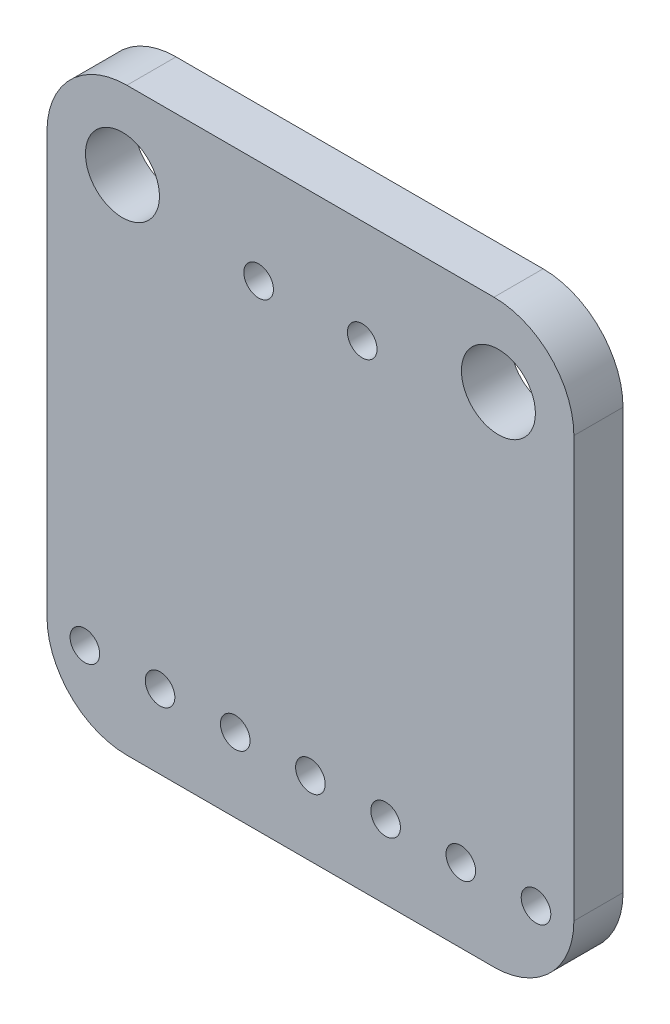
SolidWorks part; units mm, degrees
ref_plane "Front" through (0, 0, 0) normal (0, 0, 1) x (1, 0, 0)
ref_plane "Top" through (0, 0, 0) normal (0, 1, 0) x (1, 0, 0)
ref_plane "Right" through (0, 0, 0) normal (1, 0, 0) x (0, 0, -1)
sketch "Sketch1" plane through (0, 0, 0) normal (0, 0, 1) x (1, 0, 0)
  line L1 (8.9, -9.8) -> (-8.9, -9.8)
  line L2 (8.9, -9.8) -> (8.9, 9.8)
  line L3 (8.9, 9.8) -> (-8.9, 9.8)
  line L4 (-8.9, -9.8) -> (-8.9, 9.8)
  line L5 (8.9, -9.8) -> (-8.9, 9.8) construction
  line L6 (8.9, 9.8) -> (-8.9, -9.8) construction
  point P0 (0, 0)
  dimension "D1" = 17.8
  dimension "D2" = 19.6
extrude "Boss-Extrude1" add sketch "Sketch1" along normal blind 1.66
fillet "Fillet1" radius 2.7 4 edges at (8.9, 9.8, 0.83) (8.9, -9.8, 0.83) (-8.9, -9.8, 0.83) (-8.9, 9.8, 0.83)
hole_wizard "Ø2.5 (2.5) Diameter Hole1" positions "Sketch4" profile "Sketch3" hole size "Ø2.5" standard "ISO" end condition through all
sketch "Sketch4" plane through (0, 0, 1.66) normal (0, 0, 1) x (1, 0, 0)
  line L0 (0, 0) -> (0, 5.1752) construction
  line L1 (6.2, 9.8) -> (-6.2, 9.8) construction
  point P0 (-6.35, 7.1)
  point P3 (6.35, 7.1)
  dimension "D1" = 12.7
  dimension "D2" = 2.7
sketch "Sketch3" plane through (-6.35, 7.1, 1.66) normal (1, 0, 0) x (0, -1, 0)
  line L0 (0, 0) -> (0, 1.66)
  line L1 (0, 1.66) -> (1.25, 1.66)
  line L2 (1.25, 1.66) -> (1.25, 0)
  line L5 (1.25, 0) -> (0, 0)
  line L11 (0, -6.35) -> (0, 107.95) construction
  dimension "Thru Hole Dia." = 2.5
  dimension "Thru Hole Depth" = 1.66
hole_wizard "Ø1.0 (1) Diameter Hole1" positions "Sketch6" profile "Sketch5" hole size "Ø1.0" standard "ISO"
sketch "Sketch6" plane through (0, 0, 0) normal (0, 0, -1) x (-1, 0, 0)
  line L0 (0, 0) -> (0, 4.4783) construction
  line L1 (-6.2, 9.8) -> (6.2, 9.8) construction
  point P0 (-1.75, 6.3)
  point P5 (1.75, 6.3)
  dimension "D1" = 3.5
  dimension "D2" = 3.5
sketch "Sketch5" plane through (1.75, 6.3, 0) normal (1, 0, 0) x (0, 1, 0)
  line L0 (0, 0) -> (0, 32.3004)
  line L1 (0, 32.3004) -> (0.5, 32)
  line L2 (0.5, 32) -> (0.5, 0)
  line L5 (0.5, 0) -> (0, 0)
  line L10 (0, 32.3004) -> (-0.5, 32) construction
  line L11 (0, -6.35) -> (0, 107.95) construction
  dimension "Hole Dia." = 1
  dimension "Hole Depth" = 32
  dimension "Drill Angle" = 118
hole_wizard "Ø1.0 (1) Diameter Hole2" positions "Sketch8" profile "Sketch7" hole size "Ø1.0" standard "ISO"
sketch "Sketch8" plane through (0, 0, 0) normal (0, 0, -1) x (-1, 0, 0)
  line L0 (0, 0) -> (0, -12.7308) construction
  line L1 (6.2, -9.8) -> (-6.2, -9.8) construction
  point P0 (-7.62, -7.3)
  dimension "D1" = 7.62
  dimension "D2" = 2.5
sketch "Sketch7" plane through (7.62, -7.3, 0) normal (1, 0, 0) x (0, 1, 0)
  line L0 (0, 0) -> (0, 1.9604)
  line L1 (0, 1.9604) -> (0.5, 1.66)
  line L2 (0.5, 1.66) -> (0.5, 0)
  line L5 (0.5, 0) -> (0, 0)
  line L10 (0, 1.9604) -> (-0.5, 1.66) construction
  line L11 (0, -6.35) -> (0, 107.95) construction
  dimension "Hole Dia." = 1
  dimension "Hole Depth" = 1.66
  dimension "Drill Angle" = 118
pattern_linear "LPattern1" count 7 spacing 2.54 along (-1, 0, 0) of "Ø1.0 (1) Diameter Hole2"
sketch "Sketch9" plane through (0, 0, 0) normal (0, 0, -1) x (-1, 0, 0)
  line L0 (0, 0) -> (0, -2) construction
  line L1 (6.2, -9.8) -> (-6.2, -9.8) construction
  line L2 (-1.5, -3.5) -> (1.5, -3.5)
  line L3 (-1.5, -3.5) -> (-1.5, -0.5)
  line L4 (-1.5, -0.5) -> (1.5, -0.5)
  line L5 (1.5, -3.5) -> (1.5, -0.5)
  line L6 (-1.5, -3.5) -> (1.5, -0.5) construction
  line L7 (-1.5, -0.5) -> (1.5, -3.5) construction
  dimension "D1" = 3
  dimension "D2" = 6.3
extrude "Boss-Extrude2" add sketch "Sketch9" along normal blind 1.2
sketch "Sketch10" plane through (0, 0, 0) normal (0, 0, -1) x (-1, 0, 0)
  line L0 (0, 0) -> (0, 1.5) construction
  line L1 (-7.47, 1.5) -> (7.9833, 1.5) construction
  line L2 (3.95, 0.875) -> (1.45, 0.875)
  line L3 (-7.65, 0.875) -> (-5.15, 0.875)
  line L4 (-7.65, 0.875) -> (-7.65, 2.125)
  line L5 (-7.65, 2.125) -> (-5.15, 2.125)
  line L6 (-5.15, 0.875) -> (-5.15, 2.125)
  line L7 (-7.65, 0.875) -> (-5.15, 2.125) construction
  line L8 (-7.65, 2.125) -> (-5.15, 0.875) construction
  line L9 (-3.95, 2.125) -> (-1.45, 2.125)
  line L10 (-3.95, 2.125) -> (-3.95, 0.875)
  line L11 (-3.95, 0.875) -> (-1.45, 0.875)
  line L12 (-1.45, 2.125) -> (-1.45, 0.875)
  line L13 (1.45, 2.125) -> (1.45, 0.875)
  line L14 (3.95, 2.125) -> (1.45, 2.125)
  line L15 (3.95, 2.125) -> (3.95, 0.875)
  line L16 (5.15, 0.875) -> (5.15, 2.125)
  line L17 (7.65, 2.125) -> (5.15, 2.125)
  line L18 (7.65, 0.875) -> (7.65, 2.125)
  line L19 (7.65, 0.875) -> (5.15, 0.875)
  line L20 (3.175, -1.5) -> (7.9833, -1.5) construction
  line L21 (3.175, -0.25) -> (4.425, -0.25)
  line L22 (3.175, -0.25) -> (3.175, -2.75)
  line L23 (3.175, -2.75) -> (4.425, -2.75)
  line L24 (4.425, -0.25) -> (4.425, -2.75)
  line L25 (5.375, -0.25) -> (6.625, -0.25)
  line L26 (5.375, -0.25) -> (5.375, -2.75)
  line L27 (5.375, -2.75) -> (6.625, -2.75)
  line L28 (6.625, -0.25) -> (6.625, -2.75)
  line L29 (3.8, -0.25) -> (3.8, -2.75) construction
  point P5 (-6.4, 1.5)
  dimension "D1" = 2.5
  dimension "D2" = 1.25
  dimension "D3" = 1.5
  dimension "D4" = 6.4
  dimension "D5" = 6.2
  dimension "D6" = 3
  dimension "D7" = 3.8
  dimension "D8" = 2.2
extrude "Boss-Extrude3" add sketch "Sketch10" along normal blind 1.2
sketch "Sketch11" plane through (0, 0, 0) normal (0, 0, -1) x (-1, 0, 0)
  line L0 (8.9, 7.1) -> (8.9, -7.1) construction
  line L1 (3.6, -3.7) -> (6, -3.7)
  line L2 (3.6, -3.7) -> (3.6, -5)
  line L3 (3.6, -5) -> (6, -5)
  line L4 (6, -3.7) -> (6, -5)
  dimension "D1" = 1.3
  dimension "D2" = 3.7
  dimension "D3" = 2.9
  dimension "D4" = 3.6
extrude "Boss-Extrude4" add sketch "Sketch11" along normal blind 0.5
